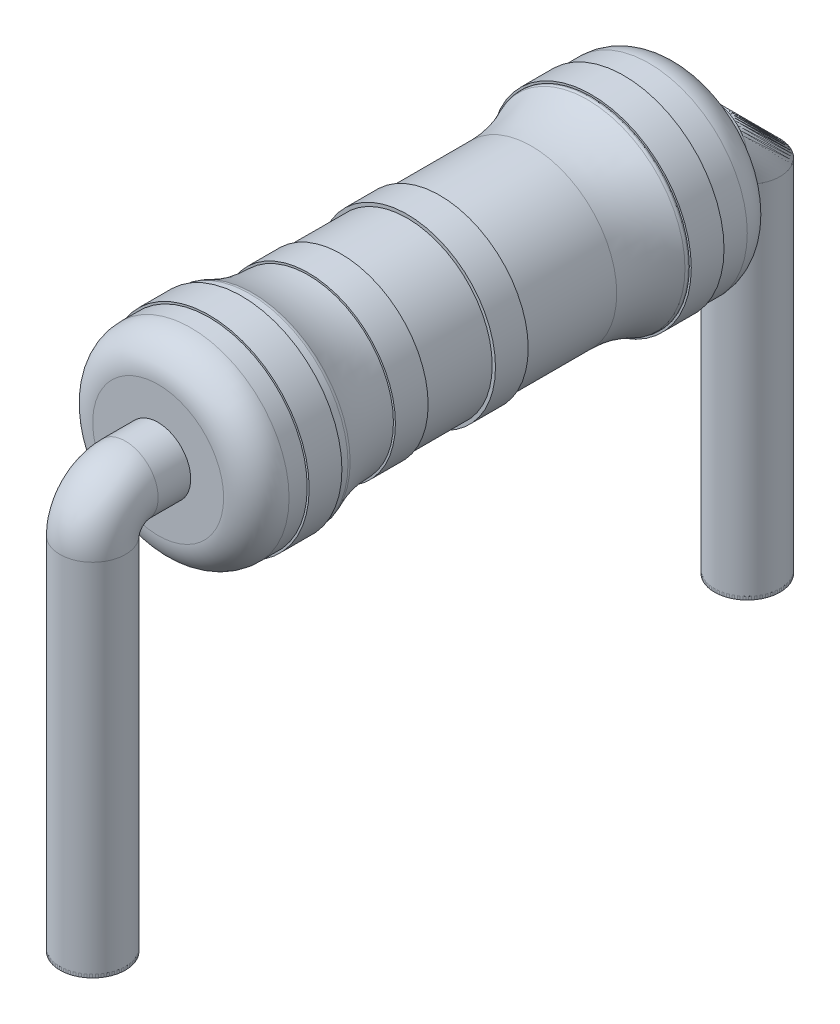
SolidWorks part; units mm, degrees
ref_plane "Front Plane" through (0, 0, 0) normal (0, 0, 1) x (1, 0, 0)
ref_plane "Top Plane" through (0, 0, 0) normal (0, 1, 0) x (1, 0, 0)
ref_plane "Right Plane" through (0, 0, 0) normal (1, 0, 0) x (0, 0, -1)
sketch "Sketch1" plane through (0, 0, 0) normal (1, 0, 0) x (0, 0, -1)
  line L0 (-30.9469, 0) -> (36.7722, 0) construction
  line L1 (2.6, 1.5) -> (3.5, 1.5)
  line L2 (-3.5, 1.5) -> (-2.6, 1.5)
  line L3 (-4, 1) -> (-4, 0)
  line L4 (-4, 0) -> (4, 0)
  line L5 (4, 1) -> (4, 0)
  line L7 (-2.5, 1.4) -> (-2.5, 1.3)
  line L8 (-2.5, 1.3) -> (2.5, 1.3)
  line L9 (2.5, 1.4) -> (2.5, 1.3)
  arc A0 (-3.5, 1.5) -> (-4, 1) centre (-3.5, 1) ccw
  arc A1 (-2.6, 1.5) -> (-2.5, 1.4) centre (-2.6, 1.4) cw
  arc A2 (2.6, 1.5) -> (2.5, 1.4) centre (2.6, 1.4) ccw
  arc A3 (3.5, 1.5) -> (4, 1) centre (3.5, 1) cw
  point P7 (0, 0)
  point P14 (0, 1.3)
  dimension "D3" = 0.5
  dimension "D6" = 0.1
  dimension "D7" = 0.5
  dimension "D1" = 8
  dimension "D2" = 1.5
  dimension "D4" = 5
  dimension "D5" = 0.2
revolve "Revolve1" add sketch "Sketch1" angle 360 about L0
fillet "Fillet1" radius 2 2 edges at (1.3, 0, -2.5) (1.3, 0, 2.5)
sketch "Sketch2" plane through (0, 0, 0) normal (1, 0, 0) x (0, 0, -1)
  line L0 (-2.1847, 0) -> (2.4452, 0) construction
  line L1 (-1.7056, -1.3) -> (-1.7056, 1.3) construction
  line L2 (-1.7056, 1.3) -> (-1.2056, 1.3)
  line L3 (-1.7056, 1.3) -> (-1.7056, 1.33)
  line L4 (-1.7056, 1.33) -> (-1.2056, 1.33)
  line L5 (-1.2056, 1.3) -> (-1.2056, 1.33)
  dimension "D1" = 0.5
revolve "Revolve2" add sketch "Sketch2" angle 360 about L0
sketch "Sketch3" plane through (0, 0, 0) normal (1, 0, 0) x (0, 0, -1)
  line L0 (-0.4894, 0) -> (0.7498, 0) construction
  line L2 (-0.1968, 1.35) -> (0.3032, 1.35)
  line L3 (-0.1968, 1.35) -> (-0.1968, 1.3)
  line L4 (-0.1968, 1.3) -> (0.3032, 1.3)
  line L5 (0.3032, 1.35) -> (0.3032, 1.3)
  dimension "D1" = 0.5
  dimension "D2" = 0.05
  dimension "D3" = 1.3
revolve "Revolve3" add sketch "Sketch3" angle 360 about L0
sketch "Sketch4" plane through (0, 0, 0) normal (1, 0, 0) x (0, 0, -1)
  line L0 (-0.4492, 0) -> (0.4962, 0) construction
  line L1 (-3.2228, 1.53) -> (-2.7228, 1.53)
  line L2 (-3.2228, 1.53) -> (-3.2228, 1.5)
  line L3 (-3.2228, 1.5) -> (-2.7228, 1.5)
  line L4 (-2.7228, 1.53) -> (-2.7228, 1.5)
  dimension "D1" = 0.5
  dimension "D2" = 0.03
  dimension "D3" = 1.5
revolve "Revolve4" add sketch "Sketch4" angle 360 about L0
sketch "Sketch5" plane through (0, 0, 0) normal (1, 0, 0) x (0, 0, -1)
  line L0 (-0.3134, 0) -> (0.3032, 0) construction
  line L1 (2.6145, 1.53) -> (3.1145, 1.53)
  line L2 (2.6145, 1.53) -> (2.6145, 1.5)
  line L3 (2.6145, 1.5) -> (3.1145, 1.5)
  line L4 (3.1145, 1.53) -> (3.1145, 1.5)
  line L5 (0.3032, -1.35) -> (0.3032, 1.35) construction
  dimension "D1" = 0.5
  dimension "D2" = 0.03
  dimension "D3" = 1.5
revolve "Revolve5" add sketch "Sketch5" angle 360 about L0
ref_plane "Plane1" through (0, 0, 4.0029) normal (0, 0, 1) x (1, 0, 0)
sketch "Sketch6" plane through (0, 0, 4.0029) normal (0, 0, 1) x (1, 0, 0)
  circle A0 centre (0, 0) radius 0.5
ref_plane "Plane2" through (0, -6, 0) normal (0, 1, 0) x (-1, 0, 0)
sketch "Sketch7" plane through (0, -6, 0) normal (0, 1, 0) x (-1, 0, 0)
  circle A0 centre (0, 5) radius 0.5
  circle A1 centre (0, 5) radius 0.5
  circle A2 centre (0, 5) radius 0.5
  dimension "D1" = 5
sketch "Sketch8" plane through (0, 0, 0) normal (1, 0, 0) x (0, 0, -1)
  line L0 (-4.0029, 0) -> (-4.5, 0)
  line L1 (-4.0029, 0.5) -> (-4.0029, -0.5) construction
  line L2 (-5, -0.5) -> (-5, -6)
  line L3 (-4.5, -6) -> (-5.5, -6) construction
  arc A0 (-4.5, 0) -> (-5, -0.5) centre (-4.5, -0.5) ccw
  dimension "D1" = 0.5
surface "Surface-Sweep1"
sketch "Sketch9" plane through (0, 0, -4) normal (0, 0, -1) x (-1, 0, 0)
  circle A0 centre (0, 0) radius 0.5
ref_plane "Plane4" through (0, -6, 0) normal (0, 1, 0) x (-1, 0, 0)
sketch "Sketch12" plane through (0, -6, 0) normal (0, 1, 0) x (-1, 0, 0)
  circle A0 centre (0, -5) radius 0.5
  dimension "D1" = 5
sketch "Sketch13" plane through (0, 0, 0) normal (1, 0, 0) x (0, 0, -1)
  line L0 (4, 0) -> (4.5, 0)
  line L1 (4, -0.5) -> (4, 0.5) construction
  line L2 (5, -0.5) -> (5, -6)
  line L3 (5.5, -6) -> (4.5, -6) construction
  arc A0 (4.5, 0) -> (5, -0.5) centre (4.5, -0.5) cw
  dimension "D1" = 0.5
surface "Surface-Sweep3"
extrude "Boss-Extrude1" add sketch "Sketch12" along normal blind 0.05 separate body
extrude "Boss-Extrude2" add sketch "Sketch7" along normal blind 0.05 separate body contours A0
